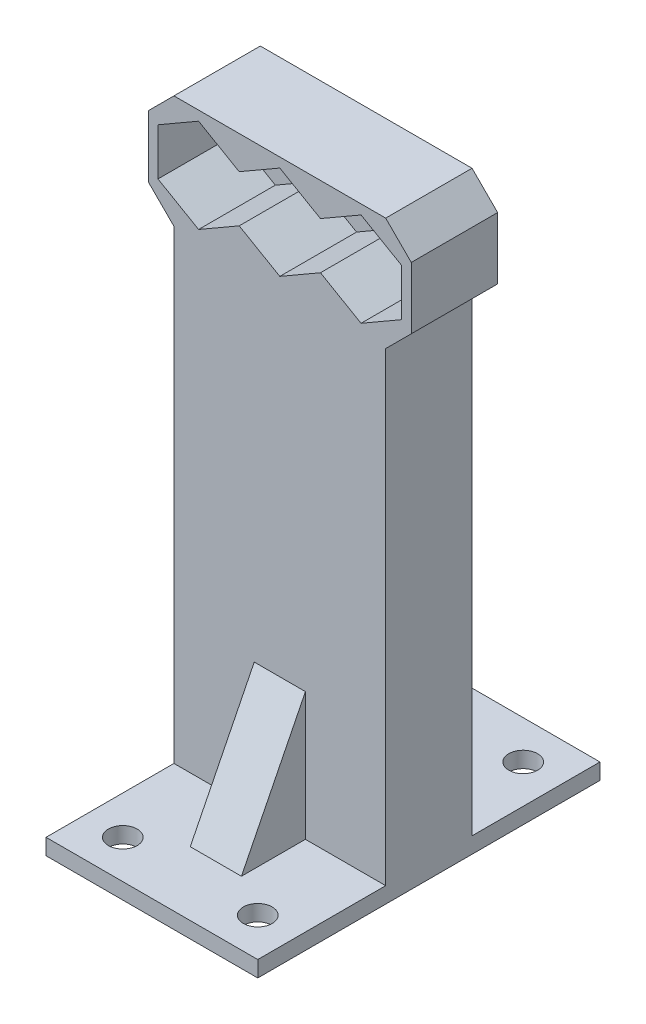
SolidWorks part; units mm, degrees
material "Custom Plastic"
ref_plane "Front Plane" through (0, 0, 0) normal (0, 0, 1) x (1, 0, 0)
ref_plane "Top Plane" through (0, 0, 0) normal (0, 1, 0) x (1, 0, 0)
ref_plane "Right Plane" through (0, 0, 0) normal (1, 0, 0) x (0, 0, -1)
sketch "Sketch1" plane through (0, 0, 0) normal (0, 0, 1) x (1, 0, 0)
  line L1 (6.35, 3.6662) -> (0, 7.3323)
  line L2 (0, 7.3323) -> (-6.35, 3.6662)
  line L3 (-6.35, 3.6662) -> (-6.35, -3.6662)
  line L4 (-6.35, -3.6662) -> (0, -7.3323)
  line L5 (0, -7.3323) -> (6.35, -3.6662)
  line L6 (6.35, -3.6662) -> (6.35, 3.6662)
  line L7 (19.05, 3.6662) -> (12.7, 7.3323)
  line L8 (12.7, 7.3323) -> (6.35, 3.6662)
  line L9 (6.35, 3.6662) -> (6.35, -3.6662)
  line L10 (6.35, -3.6662) -> (12.7, -7.3323)
  line L11 (12.7, -7.3323) -> (19.05, -3.6662)
  line L12 (19.05, -3.6662) -> (19.05, 3.6662)
  line L13 (-6.35, 3.6662) -> (-12.7, 7.3323)
  line L14 (-12.7, 7.3323) -> (-19.05, 3.6662)
  line L15 (-19.05, 3.6662) -> (-19.05, -3.6662)
  line L16 (-19.05, -3.6662) -> (-12.7, -7.3323)
  line L17 (-12.7, -7.3323) -> (-6.35, -3.6662)
  line L18 (-6.35, -3.6662) -> (-6.35, 3.6662)
  line L19 (-20.55, -8.8323) -> (20.55, -8.8323)
  line L20 (-20.55, -8.8323) -> (-20.55, 8.8323)
  line L21 (-20.55, 8.8323) -> (20.55, 8.8323)
  line L22 (20.55, -8.8323) -> (20.55, 8.8323)
  circle A0 centre (0, 0) radius 6.35 construction
  circle A1 centre (12.7, 0) radius 6.35 construction
  circle A2 centre (-12.7, 0) radius 6.35 construction
  dimension "D1" = 12.7
  dimension "D2" = 1.5
  dimension "D3" = 1.5
  dimension "D4" = 1.5
  dimension "D5" = 1.5
extrude "Boss-Extrude1" add sketch "Sketch1" along normal blind 12 contours L19 L22 L21 L20 L17 L16 L15 L14 L13 L2 L1 L8 L7 L12 L11 L10 L5 L4
sketch "Sketch2" plane through (0, 0, 0) normal (0, 0, -1) x (-1, 0, 0)
  line L1 (0, 7.3323) -> (-6.35, 3.6662)
  line L2 (-6.35, 3.6662) -> (-6.35, -3.6662)
  line L3 (-6.35, -3.6662) -> (0, -7.3323)
  line L4 (0, -7.3323) -> (6.35, -3.6662)
  line L5 (6.35, -3.6662) -> (6.35, 3.6662)
  line L6 (6.35, 3.6662) -> (0, 7.3323)
  line L7 (-12.7, 7.3323) -> (-19.05, 3.6662)
  line L8 (-19.05, 3.6662) -> (-19.05, -3.6662)
  line L9 (-19.05, -3.6662) -> (-12.7, -7.3323)
  line L10 (-12.7, -7.3323) -> (-6.35, -3.6662)
  line L11 (-6.35, -3.6662) -> (-6.35, 3.6662)
  line L12 (-6.35, 3.6662) -> (-12.7, 7.3323)
  line L13 (12.7, 7.3323) -> (6.35, 3.6662)
  line L14 (6.35, 3.6662) -> (6.35, -3.6662)
  line L15 (6.35, -3.6662) -> (12.7, -7.3323)
  line L16 (12.7, -7.3323) -> (19.05, -3.6662)
  line L17 (19.05, -3.6662) -> (19.05, 3.6662)
  line L18 (19.05, 3.6662) -> (12.7, 7.3323)
  line L19 (-20.55, 8.8323) -> (20.55, 8.8323)
  line L20 (-20.55, 8.8323) -> (-20.55, -8.8323)
  line L21 (-20.55, -8.8323) -> (20.55, -8.8323)
  line L22 (20.55, 8.8323) -> (20.55, -8.8323)
  circle A0 centre (0, 0) radius 6.35 construction
  circle A1 centre (-12.7, 0) radius 6.35 construction
  circle A2 centre (12.7, 0) radius 6.35 construction
  circle A3 centre (-12.7, 0) radius 4.75
  circle A4 centre (0, 0) radius 4.75
  circle A5 centre (12.7, 0) radius 4.75
  line M26 (12.7, -7.3323) -> (6.35, -3.6662)
  line M27 (6.35, -3.6662) -> (0, -7.3323)
  line M28 (0, -7.3323) -> (-6.35, -3.6662)
  line M29 (-6.35, -3.6662) -> (-12.7, -7.3323)
  line M30 (-12.7, -7.3323) -> (-19.05, -3.6662)
  line M31 (-19.05, -3.6662) -> (-19.05, 3.6662)
  line M32 (-19.05, 3.6662) -> (-12.7, 7.3323)
  line M33 (-12.7, 7.3323) -> (-6.35, 3.6662)
  line M34 (-6.35, 3.6662) -> (0, 7.3323)
  line M35 (0, 7.3323) -> (6.35, 3.6662)
  line M36 (6.35, 3.6662) -> (12.7, 7.3323)
  line M37 (12.7, 7.3323) -> (19.05, 3.6662)
  line M38 (19.05, 3.6662) -> (19.05, -3.6662)
  line M39 (19.05, -3.6662) -> (12.7, -7.3323)
  line M40 (-20.55, -8.8323) -> (20.55, -8.8323)
  line M41 (20.55, -8.8323) -> (20.55, 8.8323)
  line M42 (20.55, 8.8323) -> (-20.55, 8.8323)
  line M43 (-20.55, 8.8323) -> (-20.55, -8.8323)
  dimension "D1" = 9.5
  dimension "D2" = 12.7
extrude "Boss-Extrude2" add sketch "Sketch2" along normal blind 1.5 contours L2 A3 M33 M32 M31 M30 M29 | L5 L2 A4 M27 M35 M34 M28 | L5 A5 M26 M39 M38 M37 M36 | M43 M40 M41 M42 M39 M26 M27 M28 M29 M30 M31 M32 M33 M34 M35 M36 M37 M38
chamfer "Chamfer2" distance 4 angle 45 4 edges at (20.55, 8.8323, 5.25) (20.55, -8.8323, 5.25) (-20.55, -8.8323, 5.25) (-20.55, 8.8323, 5.25)
sketch "Sketch3" plane through (0, -8.8323, 0) normal (0, -1, 0) x (1, 0, 0)
  line L4 (-16.55, -1.5) -> (16.55, -1.5)
  line L5 (16.55, -1.5) -> (16.55, 12)
  line L6 (16.55, 12) -> (-16.55, 12)
  line L7 (-16.55, 12) -> (-16.55, -1.5)
  line L8 (-16.55, -1.5) -> (16.55, -1.5)
  line L9 (16.55, -1.5) -> (16.55, 12)
  line L10 (16.55, 12) -> (-16.55, 12)
  line L11 (-16.55, 12) -> (-16.55, -1.5)
  dimension "D1" = 0
extrude "Boss-Extrude3" add sketch "Sketch3" along normal blind 75.2177
sketch "Sketch4" plane through (0, -84.05, 0) normal (0, -1, 0) x (1, 0, 0)
  line L0 (-16.55, 12) -> (-16.55, -1.5) construction
  line L1 (16.55, 12) -> (-16.55, 12)
  line L2 (16.55, 12) -> (16.55, 32)
  line L3 (16.55, 32) -> (-16.55, 32)
  line L4 (-16.55, 12) -> (-16.55, 32)
  line L5 (16.55, -1.5) -> (-16.55, -1.5)
  line L6 (16.55, -1.5) -> (16.55, -21.5)
  line L7 (16.55, -21.5) -> (-16.55, -21.5)
  line L8 (-16.55, -1.5) -> (-16.55, -21.5)
  dimension "D1" = 20
extrude "Boss-Extrude4" add sketch "Sketch4" against normal blind 2.5
sketch "Sketch5" plane through (0, -81.55, 0) normal (0, 1, 0) x (1, 0, 0)
  line L0 (-10.55, -26) -> (-10.55, -32) construction
  line L1 (-10.55, -26) -> (10.55, -26) construction
  line L2 (-10.55, -26) -> (-10.55, 15.5) construction
  line L3 (-10.55, 15.5) -> (10.55, 15.5) construction
  line L4 (10.55, -26) -> (10.55, 15.5) construction
  line L5 (16.55, -32) -> (-16.55, -32) construction
  line L6 (-10.55, 15.5) -> (-10.55, 21.5) construction
  line L7 (-16.55, 21.5) -> (16.55, 21.5) construction
  line L8 (10.55, 15.5) -> (16.55, 15.5) construction
  line L9 (16.55, 21.5) -> (16.55, 1.5) construction
  line L10 (-10.55, 15.5) -> (-16.55, 15.5) construction
  line L11 (-16.55, 1.5) -> (-16.55, 21.5) construction
  circle A0 centre (-10.55, -26) radius 2.25
  circle A2 centre (10.55, -26) radius 2.25
  circle A3 centre (10.55, 15.5) radius 2.25
  circle A5 centre (-10.55, 15.5) radius 2.25
  dimension "D2" = 4.5
  dimension "D1" = 6
extrude "Cut-Extrude1" cut sketch "Sketch5" against normal up to next
sketch "Sketch6" plane through (0, 0, 0) normal (1, 0, 0) x (0, 0, -1)
  line L0 (-22, -81.55) -> (-12, -61.55)
  line L1 (-12, -81.55) -> (-32, -81.55) construction
  line L2 (-12, -81.55) -> (-12, -8.8323) construction
  dimension "D1" = 10
  dimension "D2" = 20
rib "Rib1" sketch "Sketch6" sketch "Sketch6" thickness 8 extrusion direction parallel to sketch draft on no parameters "D1"=8
sketch "Sketch7" plane through (0, 0, 0) normal (1, 0, 0) x (0, 0, -1)
  line L0 (1.5, -61.55) -> (11.5, -81.55)
  line L1 (1.5, -81.55) -> (1.5, -8.8323) construction
  line L2 (21.5, -81.55) -> (1.5, -81.55) construction
  dimension "D1" = 20
  dimension "D2" = 10
rib "Rib2" sketch "Sketch7" sketch "Sketch7" thickness 8 extrusion direction parallel to sketch draft on no parameters "D1"=8
